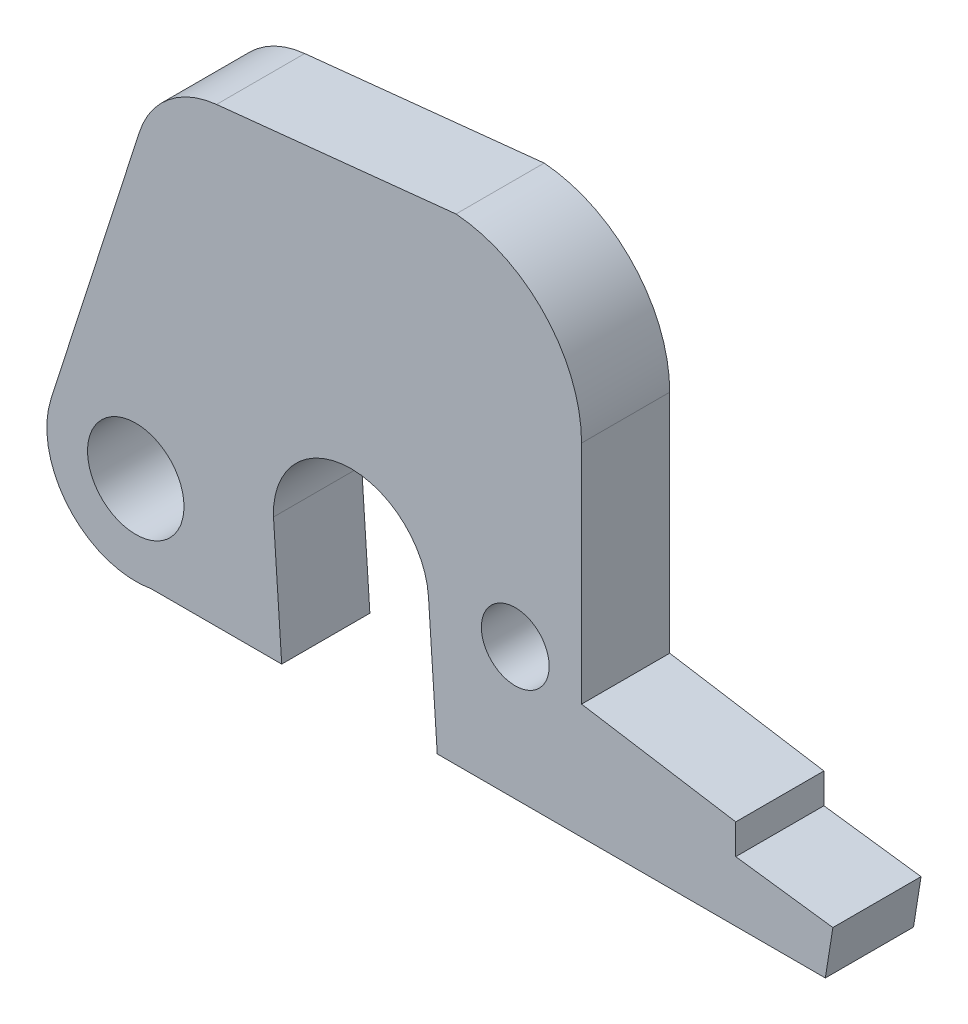
SolidWorks part; units mm, degrees
ref_plane "Front Plane" through (0, 0, 0) normal (0, 0, 1) x (1, 0, 0)
ref_plane "Top Plane" through (0, 0, 0) normal (0, 1, 0) x (1, 0, 0)
ref_plane "Right Plane" through (0, 0, 0) normal (1, 0, 0) x (0, 0, -1)
sketch "Sketch2" plane through (0, 0, 0) normal (0, 0, 1) x (1, 0, 0)
  line L0 (1.6696, -9.9207) -> (14.7506, -9.9207)
  line L1 (14.7506, -9.9207) -> (15.0046, -8.3205)
  line L2 (15.0046, -8.3205) -> (11.7307, -7.8887)
  line L3 (11.7307, -7.8887) -> (11.7307, -6.8727)
  line L4 (11.7307, -6.8727) -> (6.5339, -6.0345)
  line L5 (6.5339, -6.0345) -> (6.5339, 1.5855)
  line L6 (2.3016, 6.1575) -> (-5.7706, 5.3193)
  line L7 (-8.3713, 3.2087) -> (-11.3466, -6.0533)
  line L8 (-7.9677, -9.9207) -> (-3.5735, -9.9207)
  line L9 (1.6696, -9.9207) -> (1.3742, -5.4856)
  line L10 (-3.8503, -5.7643) -> (-3.5735, -9.9207)
  arc A0 (6.5339, 1.5855) -> (2.3016, 6.1575) centre (1.9483, 1.5855) ccw
  arc A1 (-5.7706, 5.3193) -> (-8.3713, 3.2087) centre (-5.4541, 2.2716) ccw
  arc A2 (-11.3466, -6.0533) -> (-7.9677, -9.9207) centre (-8.493, -6.9699) ccw
  arc A3 (1.3742, -5.4856) -> (-3.8503, -5.7643) centre (-1.2362, -5.6594) ccw
  circle A4 centre (-8.493, -6.9699) radius 1.6256
  circle A5 centre (4.2987, -5.4757) radius 1.143
  dimension "D1" = 2.6162
  dimension "D4" = 2.9972
  dimension "D15" = 4.5856
  dimension "D12" = 3.2512
  dimension "D17" = 2.286
  dimension "D18" = 1.0922
  dimension "D19" = 3.302
  dimension "D2" = 13.081
  dimension "D3" = 4.3942
  dimension "D5" = 4.445
  dimension "D6" = 4.1656
  dimension "D7" = 3.8862
  dimension "D8" = 3.048
  dimension "D9" = 2.032
  dimension "D10" = 0.254
  dimension "D11" = 1.6002
  dimension "D13" = 7.62
  dimension "D14" = 16.0782
  dimension "D16" = 15.24
extrude "Boss-Extrude1" add sketch "Sketch2" along normal mid plane 2.9718
